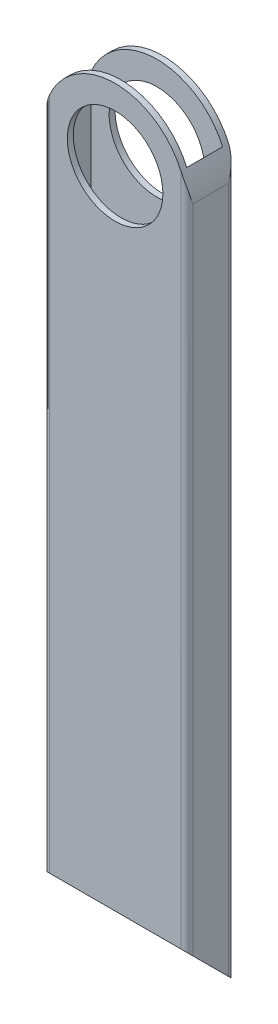
SolidWorks part; units mm, degrees
ref_plane "Front Plane" through (0, 0, 0) normal (0, 0, 1) x (1, 0, 0)
ref_plane "Top Plane" through (0, 0, 0) normal (0, 1, 0) x (1, 0, 0)
ref_plane "Right Plane" through (0, 0, 0) normal (1, 0, 0) x (0, 0, -1)
sketch "Sketch1" plane through (0, 0, 0) normal (0, 1, 0) x (1, 0, 0)
  line L0 (1.5875, 1.5875) -> (0, 1.5875) construction
  line L1 (1.5875, 0) -> (36.5125, 0)
  line L2 (0, 1.5875) -> (0, 11.1125)
  line L3 (1.5875, 12.7) -> (36.5125, 12.7)
  line L4 (38.1, 1.5875) -> (38.1, 11.1125)
  line L5 (1.5875, 1.5875) -> (36.5125, 1.5875)
  line L6 (1.5875, 1.5875) -> (1.5875, 11.1125)
  line L7 (1.5875, 11.1125) -> (36.5125, 11.1125)
  line L8 (36.5125, 1.5875) -> (36.5125, 11.1125)
  line L9 (1.5875, 1.5875) -> (1.5875, 0) construction
  line L10 (36.5125, 11.1125) -> (36.5125, 12.7) construction
  line L11 (36.5125, 11.1125) -> (38.1, 11.1125) construction
  arc A0 (1.5875, 0) -> (0, 1.5875) centre (1.5875, 1.5875) cw
  arc A1 (36.5125, 0) -> (38.1, 1.5875) centre (36.5125, 1.5875) ccw
  arc A2 (36.5125, 12.7) -> (38.1, 11.1125) centre (36.5125, 11.1125) cw
  arc A3 (0, 11.1125) -> (1.5875, 12.7) centre (1.5875, 11.1125) cw
  point P16 (0, 0)
  point P19 (38.1, 0)
  point P22 (38.1, 12.7)
  point P25 (0, 12.7)
  dimension "D4" = 1.5875
  dimension "D1" = 38.1
  dimension "D2" = 12.7
  dimension "D3" = 1.5875
extrude "Boss-Extrude1" add sketch "Sketch1" along normal blind 203.2
sketch "Sketch2" plane through (0, 0, 0) normal (0, 0, 1) x (1, 0, 0)
  line L0 (38.1, 203.2) -> (38.1, 0) construction
  line L2 (1.5875, 203.2) -> (36.5125, 203.2) construction
  line L3 (38.1, 203.2) -> (38.1, 0) construction
  line L4 (0, 184.15) -> (0, 209.55)
  line L6 (38.1, 209.55) -> (38.1, 184.15)
  line L7 (0, 209.55) -> (38.1, 209.55)
  circle A2 centre (19.05, 184.15) radius 12.7
  arc A3 (0, 184.15) -> (38.1, 184.15) centre (19.05, 184.15) cw
  dimension "D1" = 19.05
  dimension "D2" = 25.4
  dimension "D8" = 6.35
  dimension "D5" = 19.05
extrude "Cut-Extrude1" cut sketch "Sketch2" against normal through all
sketch "Sketch3" plane through (38.1, 0, 0) normal (1, 0, 0) x (0, 0, -1)
  line L0 (0, 0) -> (12.7, 0)
  line L1 (12.7, 0) -> (0, 12.7)
  line L2 (0, 191.7634) -> (0, 0) construction
  line L3 (0, 12.7) -> (0, 0)
extrude "Cut-Extrude2" cut sketch "Sketch3" against normal through all
